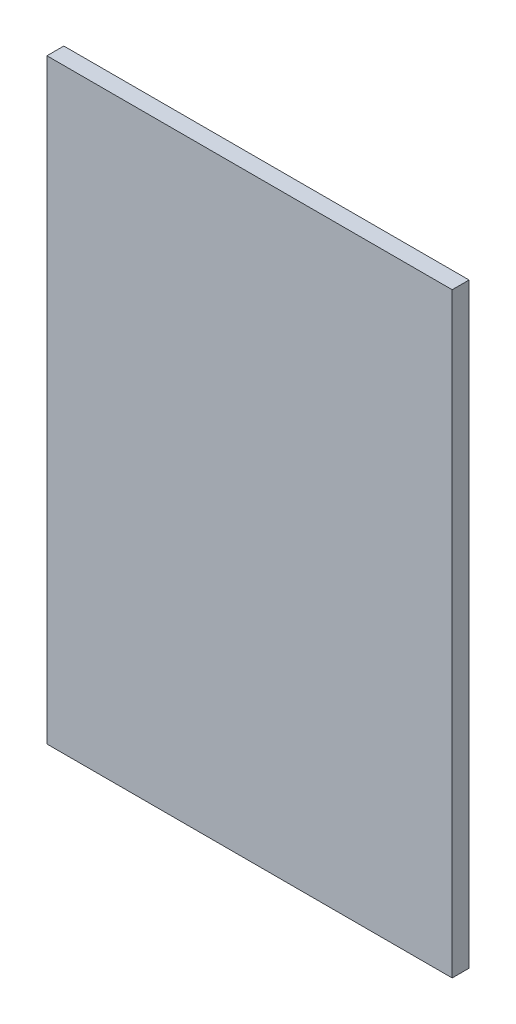
SolidWorks part; units mm, degrees
ref_plane "Front Plane" through (0, 0, 0) normal (0, 0, 1) x (1, 0, 0)
ref_plane "Top Plane" through (0, 0, 0) normal (0, 1, 0) x (1, 0, 0)
ref_plane "Right Plane" through (0, 0, 0) normal (1, 0, 0) x (0, 0, -1)
sketch "Sketch1" plane through (0, 0, 0) normal (0, 0, 1) x (1, 0, 0)
  line L1 (-60, -90) -> (60, -90)
  line L2 (-60, -90) -> (-60, 90)
  line L3 (-60, 90) -> (60, 90)
  line L4 (60, -90) -> (60, 90)
  line L5 (-60, -90) -> (60, 90) construction
  line L6 (-60, 90) -> (60, -90) construction
  point P0 (0, 0)
  dimension "D1" = 120
  dimension "D2" = 180
extrude "Boss-Extrude1" add sketch "Sketch1" along normal blind 5
sketch "Sketch2" plane through (0, 0, 0) normal (0, 0, -1) x (-1, 0, 0)
  line L0 (60, -90) -> (-60, -90) construction
  line L1 (-7, 70) -> (-15, 70)
  line L2 (-7, 70) -> (-7, -70)
  line L3 (-7, -70) -> (-15, -70)
  line L4 (-15, 70) -> (-15, -70)
  line L5 (7, 70) -> (15, 70)
  line L6 (7, 70) -> (7, -70)
  line L7 (7, -70) -> (15, -70)
  line L8 (15, 70) -> (15, -70)
  line L9 (-60, 90) -> (60, 90) construction
  line L10 (0, 0) -> (-15, 0) construction
  line L11 (0, 0) -> (15, 0) construction
  dimension "D1" = 20
  dimension "D2" = 20
  dimension "D3" = 8
  dimension "D4" = 8
  dimension "D5" = 14
extrude "Boss-Extrude2" add sketch "Sketch2" along normal blind 14
sketch "Sketch3" plane through (0, 0, 0) normal (0, 0, -1) x (-1, 0, 0)
  line L0 (60, 90) -> (60, -90) construction
  line L1 (-60, 90) -> (60, 90)
  line L2 (-60, 90) -> (-60, 86.5)
  line L3 (-60, 86.5) -> (60, 86.5)
  line L4 (60, 90) -> (60, 86.5)
  dimension "D1" = 3.5
extrude "Cut-Extrude1" cut sketch "Sketch3" against normal blind 10
